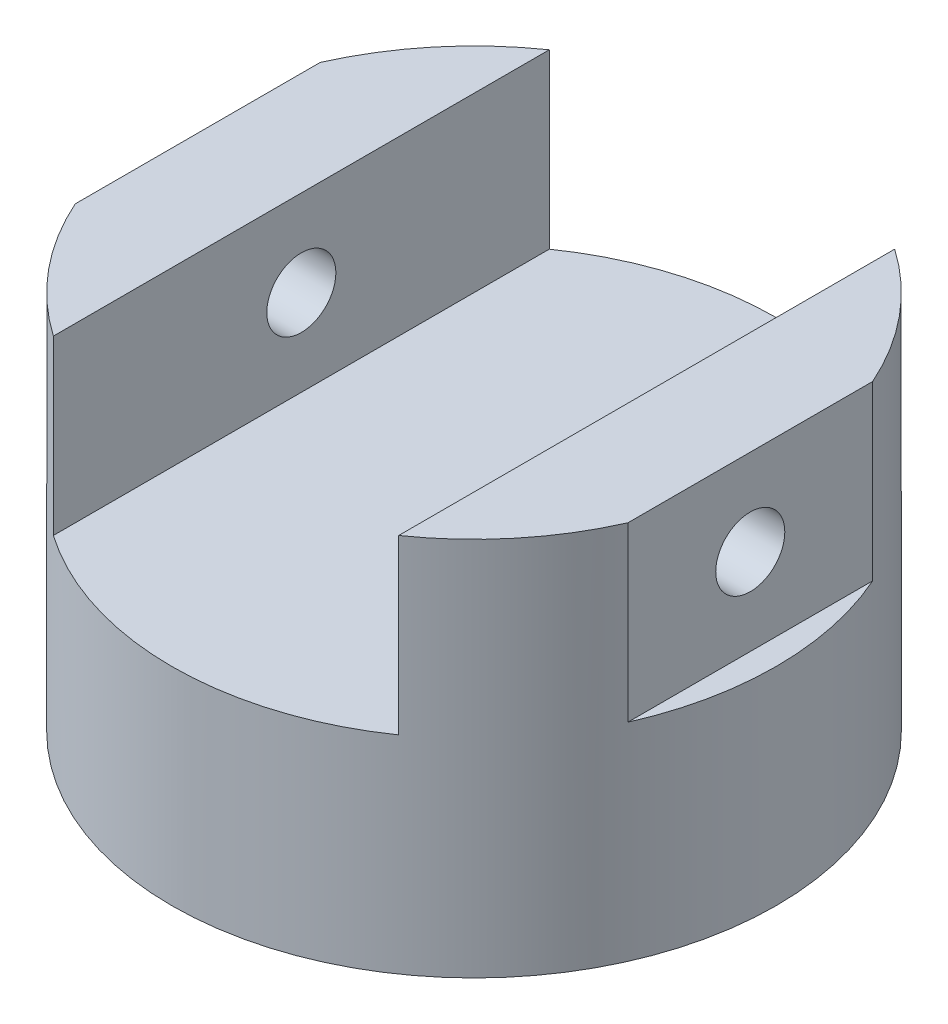
SolidWorks part; units mm, degrees
ref_plane "Plano frontal" through (0, 0, 0) normal (0, 0, 1) x (1, 0, 0)
ref_plane "Plano superior" through (0, 0, 0) normal (0, 1, 0) x (1, 0, 0)
ref_plane "Plano direito" through (0, 0, 0) normal (1, 0, 0) x (0, 0, -1)
sketch "Esboço1" plane through (0, 0, 0) normal (0, 0, 1) x (1, 0, 0)
  line L0 (0, 0) -> (0, 323.5206) construction
  line L1 (0, 0) -> (75, 0) construction
  line L2 (0, 260) -> (175, 260)
  line L3 (175, 260) -> (175, 40)
  line L4 (75, 0) -> (0, 0)
  line L5 (0, 0) -> (0, 260)
  line L6 (175, 40) -> (75, 40)
  line L7 (75, 40) -> (75, 0)
  line L8 (175, 0) -> (409.5885, 0) construction
  point P10 (0, 0)
  dimension "D1" = 350
  dimension "D2" = 260
  dimension "D3" = 40
  dimension "D4" = 150
revolve "Revolução1" add sketch "Esboço1" angle 360 about L0
sketch "Esboço2" plane through (0, 0, 0) normal (0, 0, 1) x (1, 0, 0)
  line L0 (0, 0) -> (0, 260) construction
  line L1 (175, 260) -> (-175, 260) construction
  line L2 (100, 260) -> (100, 160)
  line L3 (100, 160) -> (-100, 160)
  line L4 (160, 260) -> (160, 160)
  line L5 (160, 160) -> (175, 160)
  line L6 (175, 40) -> (175, 260) construction
  line L7 (175, 160) -> (175, 260)
  line L8 (175, 260) -> (160, 260)
  line L9 (100, 160) -> (160, 160) construction
  line L10 (100, 260) -> (-100, 260)
  line L11 (-175, 260) -> (-160, 260)
  line L12 (-175, 160) -> (-175, 260)
  line L13 (-160, 160) -> (-175, 160)
  line L14 (-160, 260) -> (-160, 160)
  line L15 (-100, 160) -> (-160, 160) construction
  line L16 (-100, 260) -> (-100, 160)
  point P20 (0, 160)
  dimension "D1" = 200
  dimension "D2" = 320
  dimension "D3" = 100
extrude "Corte-extrusão1" cut sketch "Esboço2" against normal through all both and the other way through all
sketch "Esboço3" plane through (160, 0, 0) normal (1, 0, 0) x (0, 0, -1)
  line L0 (0, 260) -> (0, 160) construction
  line L1 (70.8872, 260) -> (-70.8872, 260) construction
  line L2 (70.8872, 160) -> (-70.8872, 160) construction
  circle A0 centre (0, 210) radius 20
  dimension "D1" = 40
extrude "Corte-extrusão2" cut sketch "Esboço3" against normal through all both and the other way through all
